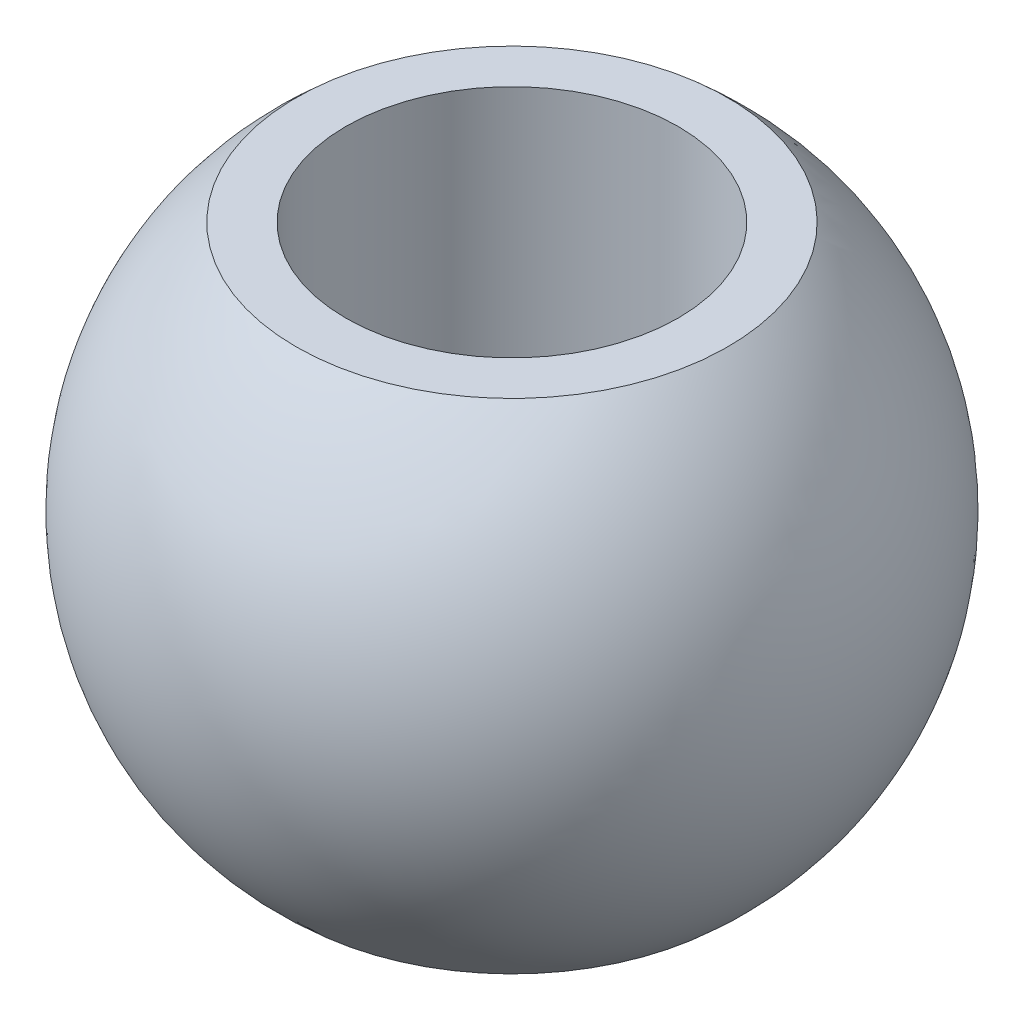
SolidWorks part; units mm, degrees
material "Chrome Stainless Steel"
ref_plane "Front Plane" through (0, 0, 0) normal (0, 0, 1) x (1, 0, 0)
ref_plane "Top Plane" through (0, 0, 0) normal (0, 1, 0) x (1, 0, 0)
ref_plane "Right Plane" through (0, 0, 0) normal (1, 0, 0) x (0, 0, -1)
sketch "Sketch1" plane through (0, 0, 0) normal (0, 1, 0) x (1, 0, 0)
  line L0 (7.9375, 0) -> (-7.9375, 0)
  arc A0 (7.9375, 0) -> (-7.9375, 0) centre (0, 0) cw
  dimension "D1" = 7.9375
revolve "Revolve1" add sketch "Sketch1" angle 360 about L0
sketch "Sketch2" plane through (0, 0, 0) normal (0, 1, 0) x (1, 0, 0)
  circle A0 centre (0, 0) radius 4
  dimension "D1" = 8
extrude "Cut-Extrude1" cut sketch "Sketch2" against normal through all both and the other way through all
sketch "Sketch3" plane through (0, 0, 0) normal (1, 0, 0) x (0, 0, -1)
  line L1 (-7.9375, -6) -> (7.9375, -6)
  line L2 (-7.9375, -6) -> (-7.9375, 6)
  line L3 (-7.9375, 6) -> (7.9375, 6)
  line L4 (7.9375, -6) -> (7.9375, 6)
  line L5 (-7.9375, -6) -> (7.9375, 6) construction
  line L6 (-7.9375, 6) -> (7.9375, -6) construction
  line L7 (-15, -9) -> (15, -9)
  line L8 (-15, -9) -> (-15, 9)
  line L9 (-15, 9) -> (15, 9)
  line L10 (15, -9) -> (15, 9)
  line L11 (-15, -9) -> (15, 9) construction
  line L12 (-15, 9) -> (15, -9) construction
  point P0 (0, 0)
  point P5 (0, 0)
  dimension "D1" = 12
  dimension "D2" = 15.875
  dimension "D3" = 18
  dimension "D4" = 15.875
  dimension "D5" = 30
extrude "Cut-Extrude2" cut sketch "Sketch3" against normal through all both and the other way through all
equation "\"Bd\"= 15.875"
equation "\"di\"= 8"
equation "\"D1@Sketch1\"=\"Bd\"/2"
equation "\"D2@Sketch3\"=\"Bd\""
equation "\"B1\"= 12''"
equation "\"D1@Sketch3\"=\"B1\""
equation "\"D1@Sketch2\"=\"di\""
